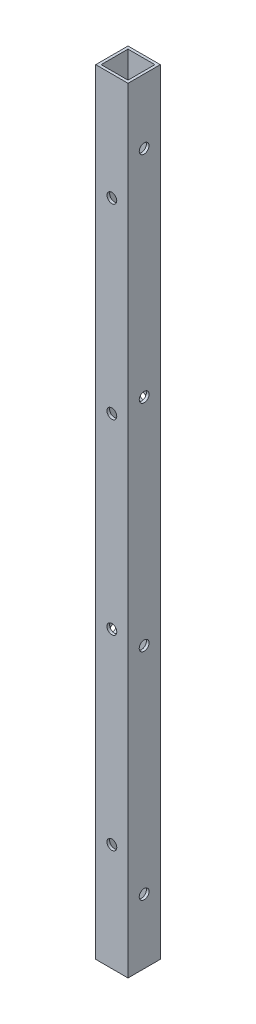
SolidWorks part; units mm, degrees
material "1060 Alloy"
ref_plane "Front Plane" through (0, 0, 0) normal (0, 0, 1) x (1, 0, 0)
ref_plane "Top Plane" through (0, 0, 0) normal (0, 1, 0) x (1, 0, 0)
ref_plane "Right Plane" through (0, 0, 0) normal (1, 0, 0) x (0, 0, -1)
sketch "Sketch1" plane through (0, 0, 0) normal (0, 1, 0) x (1, 0, 0)
  line L1 (-9.525, 9.525) -> (9.525, 9.525)
  line L2 (-9.525, 9.525) -> (-9.525, -9.525)
  line L3 (-9.525, -9.525) -> (9.525, -9.525)
  line L4 (9.525, 9.525) -> (9.525, -9.525)
  line L5 (-9.525, 9.525) -> (9.525, -9.525) construction
  line L6 (-9.525, -9.525) -> (9.525, 9.525) construction
  line L7 (-7.9375, 7.9375) -> (7.9375, 7.9375)
  line L8 (-7.9375, 7.9375) -> (-7.9375, -7.9375)
  line L9 (-7.9375, -7.9375) -> (7.9375, -7.9375)
  line L10 (7.9375, 7.9375) -> (7.9375, -7.9375)
  line L11 (-7.9375, 7.9375) -> (7.9375, -7.9375) construction
  line L12 (-7.9375, -7.9375) -> (7.9375, 7.9375) construction
  point P0 (0, 0)
  point P5 (0, 0)
  dimension "D1" = 19.05
  dimension "D2" = 19.05
  dimension "D3" = 15.875
extrude "Tube" add sketch "Sketch1" along normal blind 457.4032
sketch "Sketch2" plane through (0, 0, 9.525) normal (0, 0, 1) x (1, 0, 0)
  line L0 (0, 394.0048) -> (0, 457.4032) construction
  line L2 (-9.525, 457.4032) -> (9.525, 457.4032) construction
  line L7 (0, 63.3984) -> (0, 0) construction
  circle A2 centre (0, 394.0048) radius 2.8956
  dimension "D1" = 5.7912
  dimension "D2" = 63.3984
extrude "TopPlateHoles" cut sketch "Sketch2" against normal through all
pattern_linear "LPattern1" count 4 spacing 110.2021 along (0, -1, 0) of "TopPlateHoles"
sketch "Sketch3" plane through (-9.525, 0, 0) normal (-1, 0, 0) x (0, 0, 1)
  line L0 (0, 419.3032) -> (0, 457.4032) construction
  line L1 (-9.525, 457.4032) -> (9.525, 457.4032) construction
  circle A0 centre (0, 419.3032) radius 2.8956
  dimension "D1" = 5.7912
  dimension "D2" = 38.1
extrude "SidePlateHoleMaster" cut sketch "Sketch3" against normal through all
pattern_linear "LPattern2" count 4 spacing 127.0677 along (0, -1, 0) of "SidePlateHoleMaster"
equation "\"Height\"= 32in"
equation "\"Width\"= 23in"
equation "\"Depth\"= 20in"
equation "\"Plexi\"= .121in"
equation "\"Cutwidth\"= .016in"
equation "\"Earsize\"= 1in + \"Cutwidth\" /2"
equation "\"Slotsize\" = 1in - \"CutWidth\" / 2"
equation "\"InnerWidth\" = \"Width\" - 2* \"Plexi\""
equation "\"InnerHeight\" = \"Height\" -2 * \"Plexi\""
equation "\"InnerDepth\" = \"Depth\" - 2*\"Plexi\""
equation "\"RearHoleSpacing\" = (\"Width\" - 2*\"RearHolesBorder\") / (\"RearNumHoles\"-1)"
equation "\"RivetDia\" = .228in"
equation "\"SlotDepth\" = \"Plexi\" + 0.75in + .005in"
equation "\"SideHoleSpacing\"= (\"Height\"-2*(1.75-\"Plexi\"))/5in"
equation "\"SideSlotWidth\"   = \"Plexi\"+.005in"
equation "\"SidePanelVertSpacing\" = (\"Height\"-2*(1.75-\"Plexi\")) / 5"
equation "\"BottomPanelSideHoleSpacing\" = (\"InnerDepth\"-2*(1.75-\"Plexi\")) / 4"
equation "\"Boxsize\" = .75in"
equation "\"Boxinner\" = .625in"
equation "\"CornerCube\" = 0.75in"
equation "\"RearNumHoles\" = 4"
equation "\"RearHolesBorder\" = 2.25"
equation "\"RearBarLength\" = (\"InnerWidth\"-2*\"CornerCube\")"
equation "\"RearTopNumHoles\" = 4"
equation "\"RearTopHolesBorder\" = 3.1"
equation "\"RearTopHolesSpacing\" = (\"Width\" - 2*\"RearTopHolesBorder\") / (\"RearTopNumHoles\"-1)"
equation "\"SideVertNumHoles\" = 4"
equation "\"SideVertHolesBorder\" = \"CornerCube\"+\"FingerLength\"+1.50"
equation "\"SideVertHoleSpacing\" = (\"InnerHeight\" - 2*\"SideVertHolesBorder\") / (\"SideVertNumHoles\"-1)"
equation "\"FrontDoorGap\" = .1in"
equation "\"TopDepth\" = \"Depth\"-\"DoorPlexi\"-\"FrontDoorGap\""
equation "\"MagnetThickness\"= .125in"
equation "\"MagnetDiameter\"= 12mm"
equation "\"DoorPlexi\" = \"Plexi\""
equation "\"TopBarDepth\" = \"Depth\"-\"DoorPlexi\"-\"Plexi\"-2*\"MagnetThickness\"-2*\"CornerCube\""
equation "\"D1@Tube\"=\"TopBarDepth\""
equation "\"D1@Sketch2\"=\"RivetDia\""
equation "\"SideTopNumHoles\" = 4"
equation "\"SideTopHoleOffset\"=\"CornerCube\"+\"FingerLength\"+\"Plexi\"+.5"
equation "\"SideTopHoleSpacing\" = (\"TopBarDepth\"-2*\"SideTopHoleOffset\") / (\"SideTopNumHoles\"-1)"
equation "\"D2@Sketch2\"=\"SideTopHoleOffset\""
equation "\"FingerLength\" = 1.125in"
equation "\"D3@LPattern1\"=\"SideTopHoleSpacing\""
equation "\"D1@LPattern1\"=\"SideTopNumHoles\""
equation "\"D1@Sketch3\"=\"RivetDia\""
equation "\"SideHorizNumHoles\" = 4"
equation "\"SideHorizHoleBorder\" = 1.50"
equation "\"SideHorizHoleSpacing\" = (\"TopBarDepth\"-2*\"SideHorizHoleBorder\") / (\"SideHorizNumHoles\"-1)"
equation "\"D2@Sketch3\"=\"SideHorizHoleBorder\""
equation "\"D3@LPattern2\"=\"SideHorizHoleSpacing\""
equation "\"D1@LPattern2\"=\"SideHorizNumHoles\""
equation "\"D3@Sketch1\"=\"Boxinner\""
